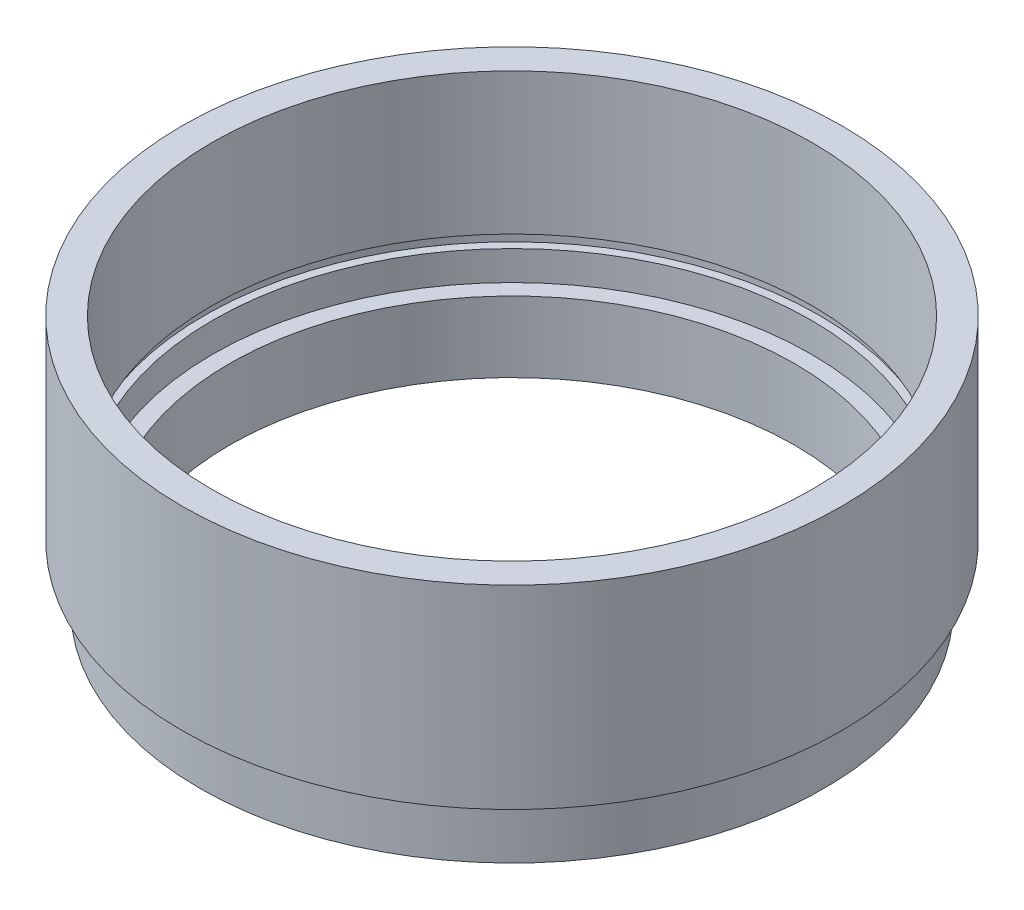
SolidWorks part; units mm, degrees
ref_plane "前视基准面" through (0, 0, 0) normal (0, 0, 1) x (1, 0, 0)
ref_plane "上视基准面" through (0, 0, 0) normal (0, 1, 0) x (1, 0, 0)
ref_plane "右视基准面" through (0, 0, 0) normal (1, 0, 0) x (0, 0, -1)
sketch "草图1" plane through (0, 0, 0) normal (0, 0, 1) x (1, 0, 0)
  line L0 (0, 0) -> (0, 21.8535) construction
  line L1 (24, 0) -> (26.5, 0)
  line L2 (26.5, 0) -> (26.5, 4)
  line L3 (26.5, 4) -> (25.5, 4)
  line L4 (25.5, 4) -> (25.5, 5)
  line L5 (25.5, 5) -> (28, 5)
  line L6 (28, 5) -> (28, 21.5)
  line L7 (28, 21.5) -> (25.5, 21.5)
  line L8 (25.5, 21.5) -> (25.5, 9.5)
  line L9 (25.5, 9.5) -> (26.1, 9.5)
  line L10 (26.1, 9.5) -> (26.1, 8.5)
  line L11 (26.1, 8.5) -> (25.4, 8.5)
  line L12 (25.4, 8.5) -> (25.4, 6)
  line L13 (25.4, 6) -> (24, 6)
  line L14 (24, 0) -> (24, 6)
  dimension "D1" = 21.5
  dimension "D2" = 28
  dimension "D3" = 25.5
  dimension "D4" = 25.4
  dimension "D5" = 1
  dimension "D6" = 2.5
  dimension "D7" = 24
  dimension "D8" = 26.5
  dimension "D9" = 1
  dimension "D10" = 5
  dimension "D11" = 6
  dimension "D12" = 26.1
  dimension "D13" = 25.5
revolve "旋转1" add sketch "草图1" angle 360 about L0
cosmetic thread "装饰螺纹线11" parameters "D2"=52
cosmetic thread "装饰螺纹线12" parameters "D2"=52
